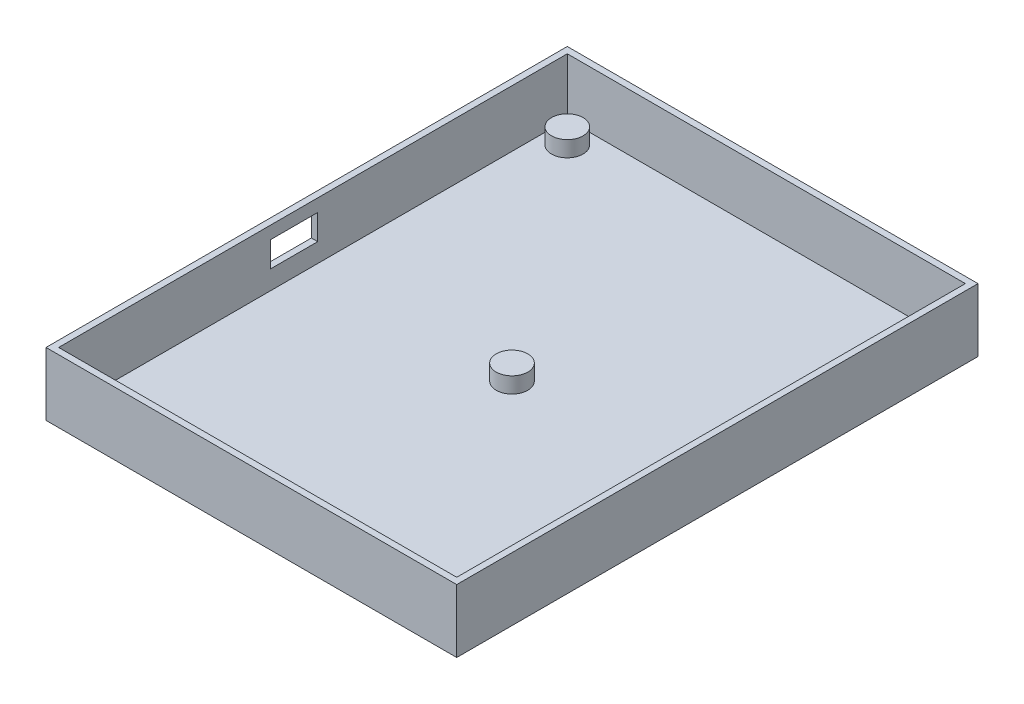
SolidWorks part; units mm, degrees
ref_plane "Front Plane" through (0, 0, 0) normal (0, 0, 1) x (1, 0, 0)
ref_plane "Top Plane" through (0, 0, 0) normal (0, 1, 0) x (1, 0, 0)
ref_plane "Right Plane" through (0, 0, 0) normal (1, 0, 0) x (0, 0, -1)
sketch "Sketch1" plane through (0, 0, 0) normal (0, 1, 0) x (1, 0, 0)
  line L1 (-32.5, -41.25) -> (32.5, -41.25)
  line L2 (-32.5, -41.25) -> (-32.5, 41.25)
  line L3 (-32.5, 41.25) -> (32.5, 41.25)
  line L4 (32.5, -41.25) -> (32.5, 41.25)
  line L5 (-32.5, -41.25) -> (32.5, 41.25) construction
  line L6 (-32.5, 41.25) -> (32.5, -41.25) construction
  point P0 (0, 0)
  dimension "D1" = 65
  dimension "D2" = 82.5
extrude "Boss-Extrude1" add sketch "Sketch1" along normal blind 10
sketch "Sketch2" plane through (0, 10, 0) normal (0, 1, 0) x (1, 0, 0)
  line L0 (-31.5, 40.25) -> (-31.5, -40.25)
  line L1 (-31.5, -40.25) -> (31.5, -40.25)
  line L2 (31.5, -40.25) -> (31.5, 40.25)
  line L3 (31.5, 40.25) -> (-31.5, 40.25)
  line L4 (-32.5, 41.25) -> (-32.5, -41.25) construction
  line L5 (32.5, 41.25) -> (-32.5, 41.25) construction
  line L6 (32.5, -41.25) -> (32.5, 41.25) construction
  line L7 (-32.5, -41.25) -> (32.5, -41.25) construction
  dimension "D1" = 1
  dimension "D2" = 1
  dimension "D3" = 1
  dimension "D4" = 1
extrude "Cut-Extrude1" cut sketch "Sketch2" against normal blind 9
sketch "Sketch4" plane through (0, 1, 0) normal (0, 1, 0) x (1, 0, 0)
  line L0 (31.5, 40.25) -> (-31.5, 40.25) construction
  line L1 (-31.5, 40.25) -> (-31.5, -40.25) construction
  line L2 (31.5, -40.25) -> (31.5, 40.25) construction
  line L3 (31.5, 40.25) -> (-31.5, 40.25) construction
  line L4 (-31.5, -40.25) -> (31.5, -40.25) construction
  line L5 (-31.5, 40.25) -> (-31.5, -40.25) construction
  circle A0 centre (-28, 36.75) radius 2.5
  circle A1 centre (28, 36.75) radius 2.5
  circle A4 centre (-28, -36.75) radius 2.5
  circle A5 centre (28, -36.75) radius 2.5
  circle A6 centre (0, 0) radius 2.5
  dimension "D1" = 5
  dimension "D2" = 5
  dimension "D3" = 5
  dimension "D4" = 5
  dimension "D13" = 5
  dimension "D5" = 3.5
  dimension "D6" = 3.5
  dimension "D7" = 3.5
  dimension "D8" = 3.5
  dimension "D9" = 3.5
  dimension "D10" = 3.5
  dimension "D11" = 3.5
  dimension "D12" = 3.5
extrude "Boss-Extrude2" add sketch "Sketch4" along normal blind 2.5
sketch "Sketch5" plane through (-32.5, 0, 0) normal (-1, 0, 0) x (0, 0, 1)
  line L0 (41.25, 10) -> (41.25, 0) construction
  line L1 (-0.75, 8) -> (6.75, 8)
  line L2 (-0.75, 8) -> (-0.75, 4)
  line L3 (-0.75, 4) -> (6.75, 4)
  line L4 (6.75, 8) -> (6.75, 4)
  line L5 (-41.25, 0) -> (41.25, 0) construction
  dimension "D1" = 34.5
  dimension "D2" = 7.5
  dimension "D3" = 4
  dimension "D4" = 4
extrude "Cut-Extrude2" cut sketch "Sketch5" against normal blind 1
